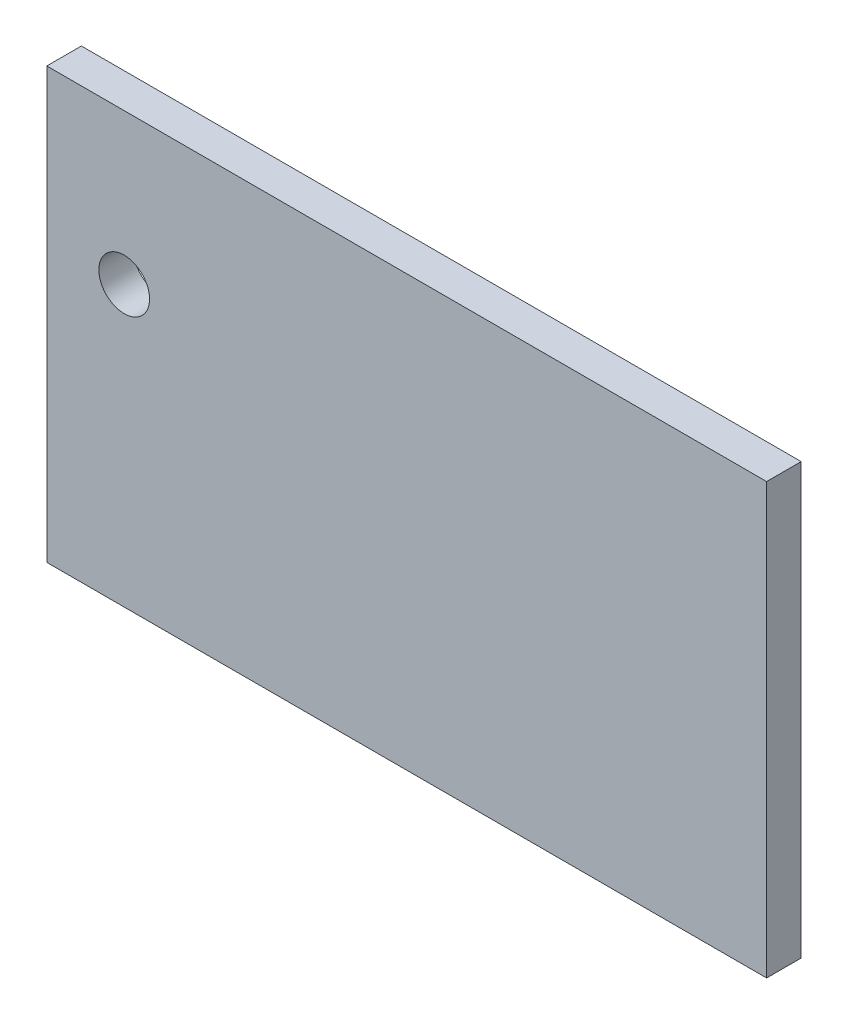
SolidWorks part; units mm, degrees
ref_plane "Front Plane" through (0, 0, 0) normal (0, 0, 1) x (1, 0, 0)
ref_plane "Top Plane" through (0, 0, 0) normal (0, 1, 0) x (1, 0, 0)
ref_plane "Right Plane" through (0, 0, 0) normal (1, 0, 0) x (0, 0, -1)
sketch "Sketch1" plane through (0, 0, 0) normal (0, 0, 1) x (1, 0, 0)
  line L1 (0, 0) -> (127.7391, 0)
  line L2 (0, 0) -> (0, 76.296)
  line L3 (0, 76.296) -> (127.7391, 76.296)
  line L4 (127.7391, 0) -> (127.7391, 76.296)
extrude "Boss-Extrude1" add sketch "Sketch1" along normal blind 6.135
sketch "Sketch2" plane through (0, 0, 6.135) normal (0, 0, 1) x (1, 0, 0)
  circle A0 centre (13.7348, 49.5909) radius 4.5
extrude "Cut-Extrude1" cut sketch "Sketch2" against normal through all
